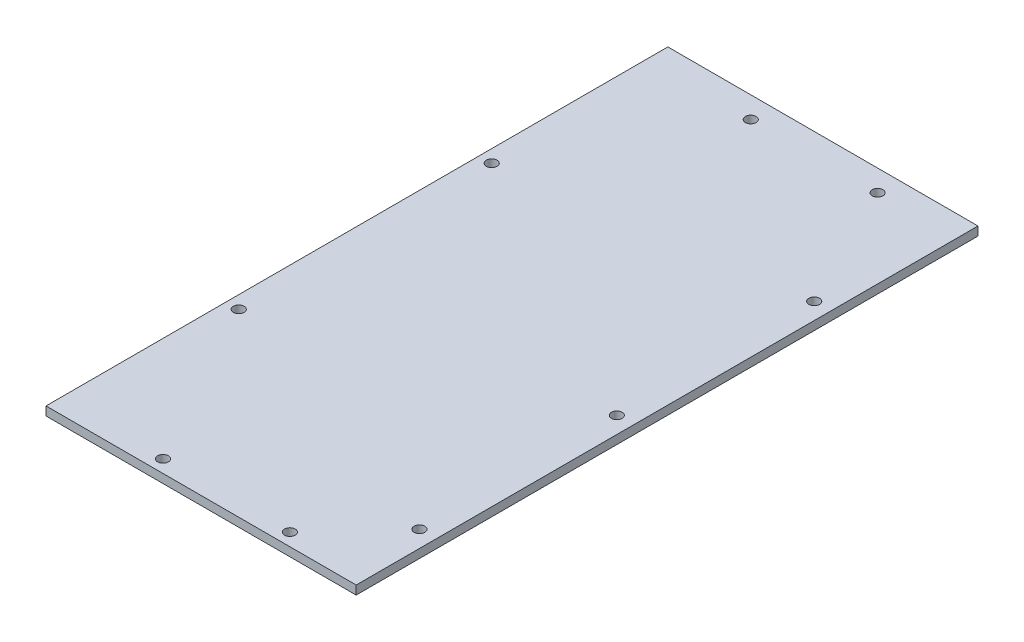
SolidWorks part; units mm, degrees
ref_plane "Front Plane" through (0, 0, 0) normal (0, 0, 1) x (1, 0, 0)
ref_plane "Top Plane" through (0, 0, 0) normal (0, 1, 0) x (1, 0, 0)
ref_plane "Right Plane" through (0, 0, 0) normal (1, 0, 0) x (0, 0, -1)
sketch "Sketch1" plane through (0, 0, 0) normal (0, 1, 0) x (1, 0, 0)
  line L1 (-55, 110.2663) -> (55, 110.2663)
  line L2 (-55, 110.2663) -> (-55, -110.2662)
  line L3 (-55, -110.2662) -> (55, -110.2662)
  line L4 (55, 110.2663) -> (55, -110.2662)
  line L5 (-55, 110.2663) -> (55, -110.2662) construction
  line L6 (-55, -110.2662) -> (55, 110.2663) construction
  point P0 (0, 0)
  dimension "D1" = 110
  dimension "D2" = 220.5325
extrude "Boss-Extrude1" add sketch "Sketch1" along normal blind 3.1
sketch "Sketch2" plane through (0, 3.1, 0) normal (0, 1, 0) x (1, 0, 0)
  point P0 (-17.9997, -105.7704)
  point P1 (27.0003, -105.7704)
  point P3 (-50.4997, -46.4113)
  point P5 (-50.4997, 43.3071)
  point P7 (-17.9997, 102.6663)
  point P9 (27.0003, 102.6663)
  point P11 (49.1, 58.075)
  point P13 (49.1, -11.925)
  point P15 (49.1, -81.925)
hole_wizard "#6 Clearance Hole1" positions "Sketch3" profile "Sketch4" hole size "#6" standard "ANSI Inch" end condition through all
sketch "Sketch3" plane through (0, 3.1, 0) normal (0, 1, 0) x (1, 0, 0)
  point P6 (49.1, 58.075)
  point P9 (49.1, -11.925)
  point P12 (49.1, -81.925)
  point P21 (-50.4997, -46.4113)
  point P24 (-50.4997, 43.3071)
sketch "Sketch4" plane through (49.1, 3.1, -58.075) normal (1, 0, 0) x (0, 0, 1)
  line L0 (0, 0) -> (0, 3.1)
  line L1 (0, 3.1) -> (1.8986, 3.1)
  line L2 (1.8986, 3.1) -> (1.8986, 0)
  line L5 (1.8986, 0) -> (0, 0)
  line L11 (0, -6.35) -> (0, 107.95) construction
  dimension "Thru Hole Dia." = 3.7973
  dimension "Thru Hole Depth" = 3.1
hole_wizard "#6 Clearance Hole3" positions "Sketch5" profile "Sketch6" hole size "#6" standard "ANSI Inch" end condition through all
sketch "Sketch5" plane through (0, 0, 0) normal (0, -1, 0) x (-1, 0, 0)
  point P0 (-27.0003, 102.6663)
  point P3 (17.9997, 102.6663)
  point P6 (-27.0003, -105.7704)
  point P9 (17.9997, -105.7704)
sketch "Sketch6" plane through (27.0003, 0, -102.6663) normal (1, 0, 0) x (0, 0, -1)
  line L0 (0, 0) -> (0, 3.1)
  line L1 (0, 3.1) -> (1.8986, 3.1)
  line L2 (1.8986, 3.1) -> (1.8986, 0)
  line L5 (1.8986, 0) -> (0, 0)
  line L11 (0, -6.35) -> (0, 107.95) construction
  dimension "Thru Hole Dia." = 3.7973
  dimension "Thru Hole Depth" = 3.1
